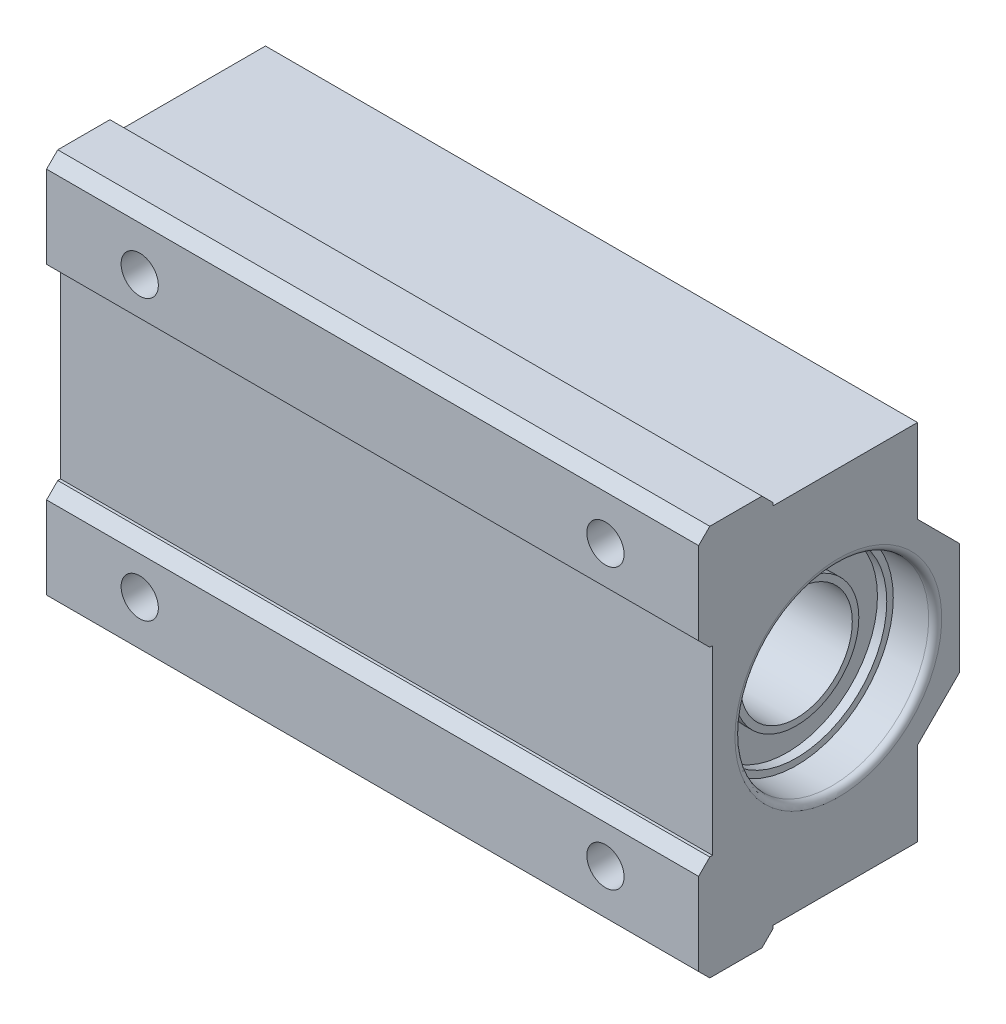
SolidWorks part; units mm, degrees
ref_plane "Alzado" through (0, 0, 0) normal (0, 0, 1) x (1, 0, 0)
ref_plane "Planta" through (0, 0, 0) normal (0, 1, 0) x (1, 0, 0)
ref_plane "Vista lateral" through (0, 0, 0) normal (1, 0, 0) x (0, 0, -1)
sketch "Croquis1" plane through (0, 0, 0) normal (0, 0, 1) x (1, 0, 0)
  line L1 (-35, -21) -> (35, -21)
  line L2 (-35, -21) -> (-35, 21)
  line L3 (-35, 21) -> (35, 21)
  line L4 (35, -21) -> (35, 21)
  line L5 (-35, -21) -> (35, 21) construction
  line L6 (-35, 21) -> (35, -21) construction
  point P0 (0, 0)
  dimension "D1" = 42
  dimension "D2" = 70
extrude "Saliente-Extruir1" add sketch "Croquis1" along normal blind 28
sketch "Croquis2" plane through (35, 0, 0) normal (1, 0, 0) x (0, 0, -1)
  line L0 (-28, 0) -> (0, 0) construction
  line L1 (-28, -21) -> (-28, 21) construction
  line L2 (-28, 9.75) -> (-26.5, 9.75)
  line L3 (-26.5, 9.75) -> (-26.5, -9.75)
  line L4 (-4.5, 21) -> (-4.5, -21) construction
  line L5 (-28, 21) -> (0, 21) construction
  line L6 (-28, -21) -> (0, -21) construction
  line L7 (-28, 19.5) -> (0, 19.5) construction
  line L8 (0, -21) -> (0, 21) construction
  line L9 (-20, 21) -> (-20, -21) construction
  line L10 (-20, 19.5) -> (-4.5, 19.5)
  line L11 (-20, 21) -> (-20, 19.5)
  line L12 (0, -6) -> (0, 6)
  line L13 (0, 6) -> (-4.5, 10.5)
  line L14 (-4.5, 10.5) -> (-4.5, 19.5)
  line L15 (0, -6) -> (-4.5, -10.5)
  line L16 (-4.5, -10.5) -> (-4.5, -19.5)
  line L17 (-20, -19.5) -> (-4.5, -19.5)
  line L18 (-20, -21) -> (-20, -19.5)
  line L19 (-28, -9.75) -> (-26.5, -9.75)
  line L20 (-28, -21) -> (0, -21)
  line L21 (-28, 21) -> (0, 21)
  line L22 (-28, -21) -> (-28, 21)
  line L23 (0, -6) -> (0, -21)
  line L24 (0, 6) -> (0, 21)
  point P30 (-26.5, 0)
  line M12 (0, -21) -> (0, 21)
  line M13 (0, 21) -> (-28, 21)
  line M14 (-28, 21) -> (-28, -21)
  line M15 (-28, -21) -> (0, -21)
  dimension "D6" = 6
  dimension "D1" = 1.5
  dimension "D2" = 9.75
  dimension "D3" = 23.5
  dimension "D4" = 1.5
  dimension "D5" = 8
  dimension "D7" = 45
extrude "Cortar-Extruir1" cut sketch "Croquis2" against normal blind 70 contours L19 L3 L2 M14 | L14 L13 L11 L10 M12 M13 | L18 L15 L16 L17 M15 M12
sketch "Croquis3" plane through (0, 0, 28) normal (0, 0, 1) x (1, 0, 0)
  line L1 (25, 15) -> (-25, 15) construction
  line L2 (25, 15) -> (25, -15) construction
  line L3 (25, -15) -> (-25, -15) construction
  line L4 (-25, 15) -> (-25, -15) construction
  line L5 (25, 15) -> (-25, -15) construction
  line L6 (25, -15) -> (-25, 15) construction
  circle A0 centre (25, -15) radius 2
  circle A1 centre (-25, -15) radius 2
  circle A2 centre (-25, 15) radius 2
  circle A3 centre (25, 15) radius 2
  point P0 (0, 0)
  dimension "D3" = 4
  dimension "D1" = 50
  dimension "D2" = 30
extrude "Cortar-Extruir2" cut sketch "Croquis3" against normal blind 70
sketch "Croquis4" plane through (35, 0, 0) normal (1, 0, 0) x (0, 0, -1)
  line L0 (-26.5, 0) -> (0, 0) construction
  line L1 (-26.5, 9.75) -> (-26.5, -9.75) construction
  line L2 (0, -6) -> (0, 6) construction
  circle A0 centre (-13, 0) radius 6
  dimension "D1" = 13
  dimension "D2" = 12
extrude "Cortar-Extruir3" cut sketch "Croquis4" against normal blind 70
sketch "Croquis5" plane through (35, 0, 0) normal (1, 0, 0) x (0, 0, -1)
  circle A0 centre (-13, 0) radius 10.4
  dimension "D1" = 20.8
extrude "Cortar-Extruir4" cut sketch "Croquis5" against normal blind 4.5
sketch "Croquis6" plane through (30.5, 0, 0) normal (1, 0, 0) x (0, 0, -1)
  circle A2 centre (-13, 0) radius 6.7
  circle A3 centre (-13, 0) radius 6.7
  circle A5 centre (-13, 0) radius 9.7
  circle A6 centre (-13, 0) radius 9.7
  dimension "D1" = 0.7
  dimension "D2" = 0.7
extrude "Cortar-Extruir5" cut sketch "Croquis6" against normal blind 1
mirror "Simetría1" about plane through (0, 0, 0) normal (1, 0, 0) of "Cortar-Extruir5", "Cortar-Extruir4"
chamfer "Chaflán1" distance 1.2 angle 45 5 edges at (0, -21, 20) (0, 21, 28) (0, -21, 28) (0, 9.75, 28) (0, -9.75, 28)
fillet "Redondeo1" radius 0.7 2 edges at (35, 0, 2.6) (-35, 0, 2.6)
